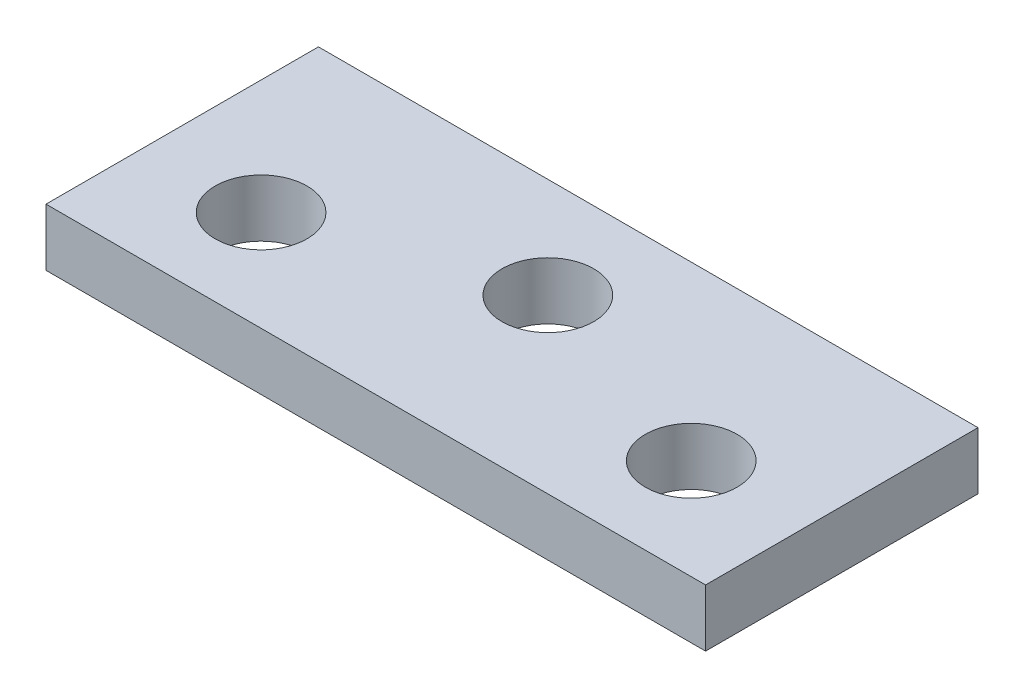
SolidWorks part; units mm, degrees
material "不锈钢 (铁素体)"
ref_plane "前视基准面" through (0, 0, 0) normal (0, 0, 1) x (1, 0, 0)
ref_plane "上视基准面" through (0, 0, 0) normal (0, 1, 0) x (1, 0, 0)
ref_plane "右视基准面" through (0, 0, 0) normal (1, 0, 0) x (0, 0, -1)
sketch "草图1" plane through (0, 0, 0) normal (0, 1, 0) x (1, 0, 0)
  line L1 (11.5, -4.75) -> (-11.5, -4.75)
  line L2 (11.5, -4.75) -> (11.5, 4.75)
  line L3 (11.5, 4.75) -> (-11.5, 4.75)
  line L4 (-11.5, -4.75) -> (-11.5, 4.75)
  line L5 (11.5, -4.75) -> (-11.5, 4.75) construction
  line L6 (11.5, 4.75) -> (-11.5, -4.75) construction
  point P0 (0, 0)
  dimension "D1" = 23
  dimension "D2" = 9.5
extrude "凸台-拉伸1" add sketch "草图1" along normal blind 2
sketch "草图2" plane through (0, 2, 0) normal (0, 1, 0) x (1, 0, 0)
  line L0 (0, 0) -> (0, 1.25) construction
  line L1 (11.5, 4.75) -> (-11.5, 4.75) construction
  line L3 (-11.5, -4.75) -> (11.5, -4.75) construction
  circle A0 centre (-7.5, -1.25) radius 1.6
  circle A1 centre (7.5, -1.25) radius 1.6
  circle A2 centre (0, 1.25) radius 1.6
  dimension "D1" = 3.2
  dimension "D2" = 3.5
  dimension "D4" = 3.5
  dimension "D3" = 15
extrude "切除-拉伸1" cut sketch "草图2" against normal through all
